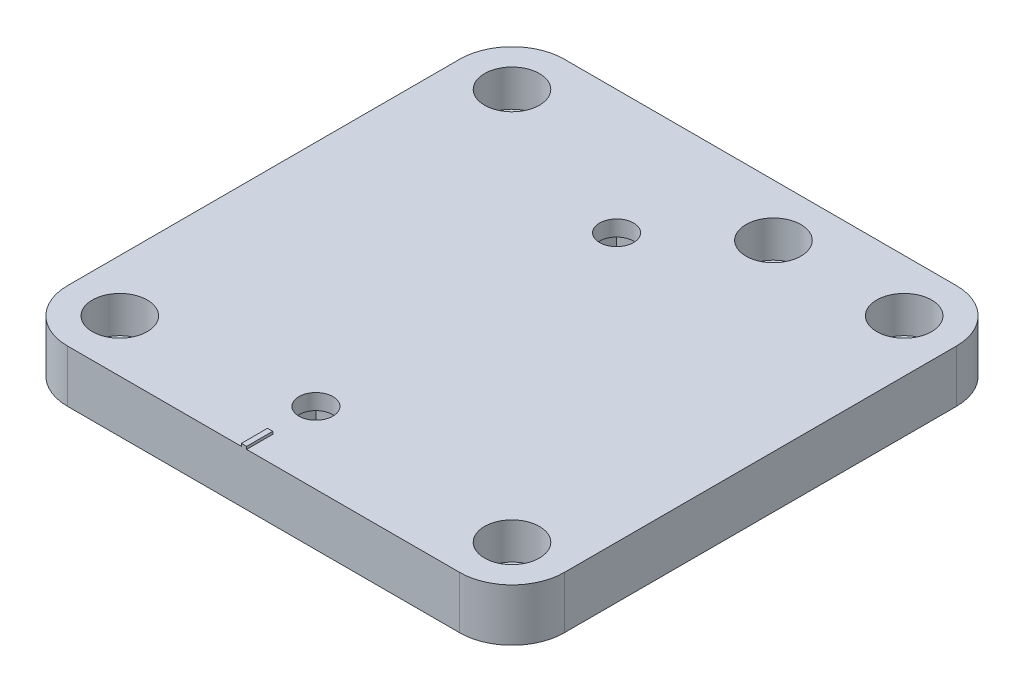
SolidWorks part; units mm, degrees
ref_plane "정면" through (0, 0, 0) normal (0, 0, 1) x (1, 0, 0)
ref_plane "윗면" through (0, 0, 0) normal (0, 1, 0) x (1, 0, 0)
ref_plane "우측면" through (0, 0, 0) normal (1, 0, 0) x (0, 0, -1)
sketch "스케치1" plane through (0, 0, 0) normal (0, 1, 0) x (1, 0, 0)
  line L2 (-43.75, 1.25) -> (-43.75, -93.75)
  line L3 (-43.75, -93.75) -> (51.25, -93.75)
  line L4 (51.25, 1.25) -> (51.25, -93.75)
  line L5 (51.25, 1.25) -> (-43.75, 1.25)
  circle A0 centre (16.25, -8.75) radius 3.2
  circle A1 centre (-33.75, -8.75) radius 3.2
  circle A6 centre (41.25, -8.75) radius 3.2
  circle A9 centre (-33.75, -83.75) radius 3.2
  circle A11 centre (41.25, -83.75) radius 3.2
  point P5 (-8.75, -8.75)
  dimension "D3" = 25
  dimension "D1" = 6.4
  dimension "D2" = 50
  dimension "D4" = 8.75
  dimension "D5" = 8.75
  dimension "D6" = 75
  dimension "D7" = 10
  dimension "D8" = 25
  dimension "D9" = 10
  dimension "D10" = 10
  dimension "D11" = 10
extrude "보스-돌출1" add sketch "스케치1" along normal blind 10
sketch "스케치2" plane through (0, 10, 0) normal (0, 1, 0) x (1, 0, 0)
  circle A0 centre (16.25, -8.75) radius 5.25
  circle A1 centre (-33.75, -8.75) radius 5.25
  circle A7 centre (41.25, -8.75) radius 5.25
  circle A9 centre (41.25, -8.75) radius 3.2 construction
  circle A12 centre (41.25, -83.75) radius 5.25
  circle A14 centre (-33.75, -83.75) radius 5.25
  dimension "D1" = 10.5
extrude "컷-돌출1" cut sketch "스케치2" against normal offset from surface (7 mm away) 3 up to face at (3.75, 0, 46.25)
fillet "필렛1" radius 10 4 edges at (-43.75, 5, -1.25) (51.25, 5, 93.75) (-43.75, 5, 93.75) (51.25, 5, -1.25)
sketch "스케치3" plane through (0, 10, 0) normal (0, 1, 0) x (1, 0, 0)
  circle A0 centre (0, -22.5) radius 3.25
  circle A1 centre (0, -80) radius 3.25
  dimension "D2" = 6.5
  dimension "D1" = 22.5
  dimension "D3" = 80
extrude "컷-돌출2" cut sketch "스케치3" against normal up to surface (10 mm away) up to face at (3.75, 0, 46.25)
sketch "스케치4" plane through (0, 0, 0) normal (0, -1, 0) x (1, 0, 0)
  line L1 (5.2, 27.7) -> (-5.2, 27.7)
  line L2 (5.2, 27.7) -> (5.2, 17.3)
  line L3 (5.2, 17.3) -> (-5.2, 17.3)
  line L4 (-5.2, 27.7) -> (-5.2, 17.3)
  line L5 (-5.2, 74.8) -> (5.2, 74.8)
  line L6 (-5.2, 74.8) -> (-5.2, 85.2)
  line L7 (-5.2, 85.2) -> (5.2, 85.2)
  line L8 (5.2, 74.8) -> (5.2, 85.2)
  circle A1 centre (0, 22.5) radius 3.25
  circle A2 centre (0, 22.5) radius 3.25 construction
  circle A3 centre (0, 80) radius 3.25
  circle A4 centre (0, 80) radius 3.25 construction
  point P8 (0, 27.7)
  point P9 (5.2, 22.5)
  point P18 (5.2, 80)
  dimension "D1" = 10.4
  dimension "D2" = 10.4
extrude "컷-돌출3" cut sketch "스케치4" against normal offset from surface (7 mm away) 3 up to face at (0, 10, 83.25)
sketch "스케치5" plane through (0, 10, 0) normal (0, 1, 0) x (1, 0, 0)
  line L0 (-33.75, -93.75) -> (41.25, -93.75) construction
  line L1 (0.5, -93.75) -> (-0.5, -93.75)
  line L2 (0.5, -93.75) -> (0.5, -88.75)
  line L3 (0.5, -88.75) -> (-0.5, -88.75)
  line L4 (-0.5, -93.75) -> (-0.5, -88.75)
  circle A0 centre (0, -80) radius 3.25 construction
  point P6 (0, -80)
  point P10 (0, -88.75)
  dimension "D1" = 1
  dimension "D2" = 5
extrude "보스-돌출2" add sketch "스케치5" along normal blind 0.5
